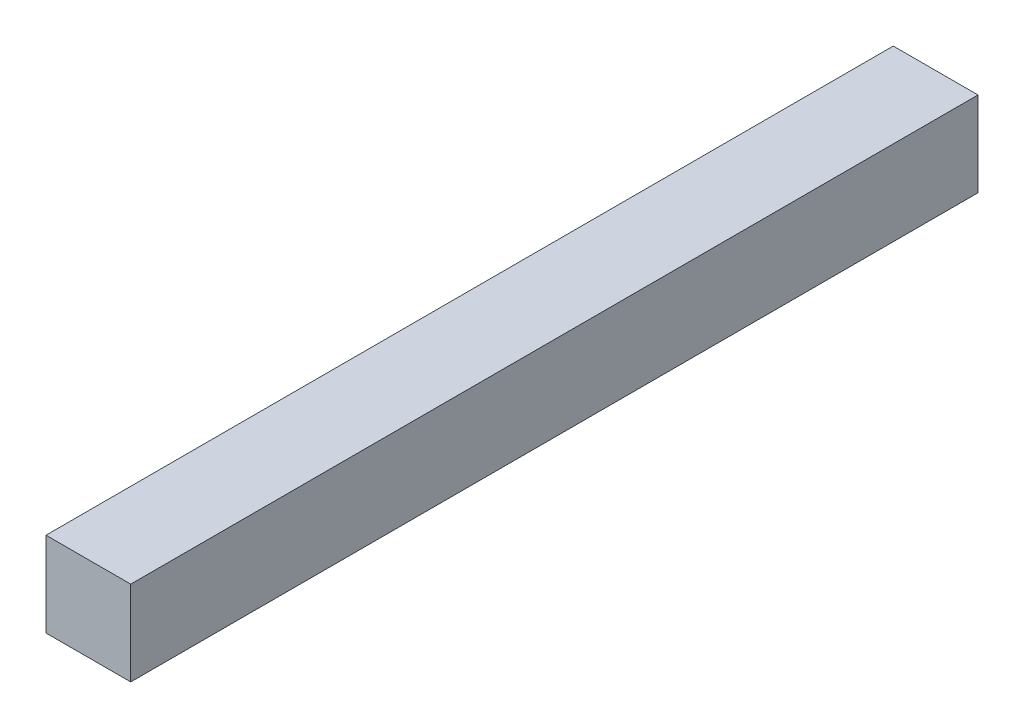
SolidWorks part; units mm, degrees
ref_plane "Front Plane" through (0, 0, 0) normal (0, 0, 1) x (1, 0, 0)
ref_plane "Top Plane" through (0, 0, 0) normal (0, 1, 0) x (1, 0, 0)
ref_plane "Right Plane" through (0, 0, 0) normal (1, 0, 0) x (0, 0, -1)
sketch "Sketch1" plane through (0, 0, 0) normal (0, 0, 1) x (1, 0, 0)
  line L1 (-1.5, 1.5) -> (1.5, 1.5)
  line L2 (-1.5, 1.5) -> (-1.5, -1.5)
  line L3 (-1.5, -1.5) -> (1.5, -1.5)
  line L4 (1.5, 1.5) -> (1.5, -1.5)
  line L5 (-1.5, 1.5) -> (1.5, -1.5) construction
  line L6 (-1.5, -1.5) -> (1.5, 1.5) construction
  point P1 (0, 0)
  dimension "D1" = 3
  dimension "D2" = 3
extrude "Boss-Extrude1" add sketch "Sketch1" along normal blind 30
